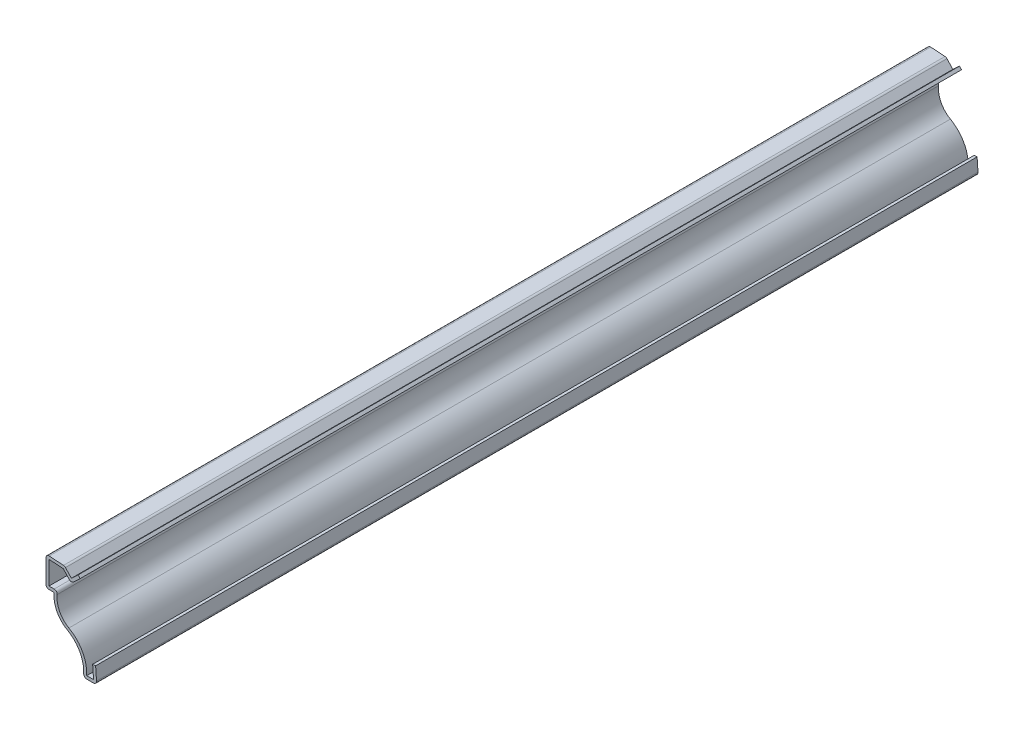
SolidWorks part; units mm, degrees
ref_plane "Front Plane" through (0, 0, 0) normal (0, 0, 1) x (1, 0, 0)
ref_plane "Top Plane" through (0, 0, 0) normal (0, 1, 0) x (1, 0, 0)
ref_plane "Right Plane" through (0, 0, 0) normal (1, 0, 0) x (0, 0, -1)
sketch "Sketch1" plane through (0, 0, 0) normal (0, 0, 1) x (1, 0, 0)
  line L0 (-0.333, 4.7625) -> (0, 0)
  line L1 (0, 0) -> (-3.9688, 0)
  line L2 (-12.6494, 17.4625) -> (-15.0813, 17.4625)
  line L3 (-15.0813, 17.4625) -> (-15.0813, 26.1937)
  line L4 (-15.0813, 26.1937) -> (-9.525, 25.8052)
  line L5 (-9.525, 25.8052) -> (-7.5406, 23.6772)
  line L6 (-7.5406, 23.6772) -> (-5.5563, 25.5277)
  arc A0 (-3.9688, 0) -> (-8.7077, 9.7413) centre (-13.3838, 1.4431) ccw
  arc A1 (-8.7077, 9.7413) -> (-12.6494, 17.4625) centre (-4.8578, 16.5735) cw
  dimension "D5" = 9.525
  dimension "D8" = 7.8422
  dimension "D1" = 26.1937
  dimension "D2" = 15.0812
  dimension "D3" = 17.4625
  dimension "D4" = 4
  dimension "D6" = 3.9688
  dimension "D7" = 2.3813
  dimension "D9" = 9.525
  dimension "D10" = 4
  dimension "D11" = 1.9844
  dimension "D12" = 0.889
  dimension "D13" = 5.5562
  dimension "D14" = 4.7625
extrude "Extrude-Thin1" add sketch "Sketch1" against normal blind 261.9375 thin
fillet "Fillet1" radius 0.889 7 edges at (0, 0, -130.9688) (-3.9688, 0, -130.9688) (-7.5845, 22.4208, -130.9688) (-11.5798, 18.3515, -130.9688) (-15.0813, 17.4625, -130.9688) (-15.0813, 26.1937, -130.9688) (-9.525, 25.8052, -130.9688)
